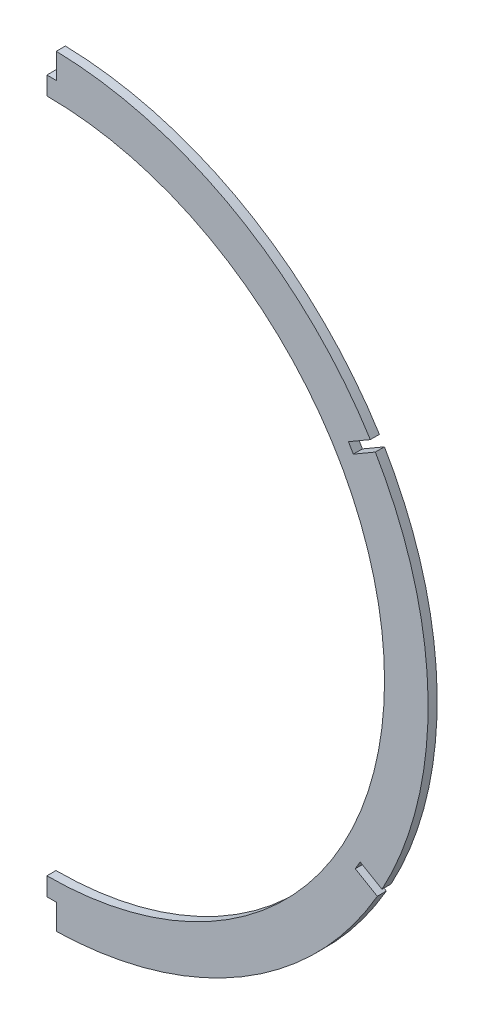
SolidWorks part; units mm, degrees
material "Plywood"
ref_plane "Front Plane" through (0, 0, 0) normal (0, 0, 1) x (1, 0, 0)
ref_plane "Top Plane" through (0, 0, 0) normal (0, 1, 0) x (1, 0, 0)
ref_plane "Right Plane" through (0, 0, 0) normal (1, 0, 0) x (0, 0, -1)
sketch "Sketch1" plane through (0, 0, 0) normal (0, 0, 1) x (1, 0, 0)
  line L0 (0, -110.0909) -> (0, -70.6286) construction
  line L1 (0, 0) -> (0, 245.1538) construction
  line L2 (0, 0) -> (0, 631.6453) construction
  line L3 (-120.188, -34.2725) -> (-93.2472, -61.2132)
  line L4 (0, 0) -> (-284.8905, 0) construction
  line L5 (-93.2472, -61.2132) -> (-94.2927, -70.7977)
  line L8 (-93.2472, -61.2132) -> (-57.7675, -96.693) construction
  arc A0 (-57.7675, -96.693) -> (-120.188, -34.2725) centre (0, 23.495) ccw
  arc A2 (-120.188, -34.2725) -> (-57.7675, -96.693) centre (0, 23.495) ccw construction
  arc A3 (-94.2927, -70.7977) -> (-57.7675, -96.693) centre (0, 23.495) ccw
  point P2 (0, 156.7839)
  point P3 (0, -109.8059)
  point P15 (-93.2472, -61.2132)
  dimension "D1" = 266.5898
  dimension "D2" = 266.7
  dimension "D3" = 23.495
  dimension "D5" = 109.22
  dimension "D6" = 45
  dimension "D7" = 38.1
extrude "Boss-Extrude1" add sketch "Sketch1" along normal mid plane 3.175
sketch "Sketch2" plane through (0, 0, 1.5875) normal (0, 0, 1) x (1, 0, 0)
  line L4 (-77.3048, -55.603) -> (-78.3203, -64.9126)
  line L5 (-107.5191, -25.3887) -> (-77.3048, -55.603)
  line L6 (-77.3048, -55.603) -> (-78.3203, -64.9126)
  line L7 (-107.5191, -25.3887) -> (-77.3048, -55.603)
  arc A2 (-78.3203, -64.9126) -> (-107.5191, -25.3887) centre (0, 23.495) ccw
  arc A3 (-78.3203, -64.9126) -> (-107.5191, -25.3887) centre (0, 23.495) ccw
  dimension "D1" = 15.24
extrude "Cut-Extrude1" cut sketch "Sketch2" against normal up to surface (3.175 mm away) up to face at (-30.5678, -4.3762, -1.5875)
fillet "Fillet1" radius 8.89 6 edges at (-107.5191, -25.3887, 0) (-120.188, -34.2725, 0) (-94.2927, -70.7977, 0) (-93.2472, -61.2132, 0) (-77.3048, -55.603, 0) (-78.3203, -64.9126, 0)
sketch "Sketch3" plane through (0, 0, 0) normal (1, 0, 0) x (0, 0, -1)
  line L1 (-107.0531, 227.715) -> (127.3903, 227.715)
  line L2 (-107.0531, 227.715) -> (-107.0531, -194.8481)
  line L3 (-107.0531, -194.8481) -> (127.3903, -194.8481)
  line L4 (127.3903, 227.715) -> (127.3903, -194.8481)
extrude "Cut-Extrude2" cut sketch "Sketch3" against normal through all
sketch "Sketch4" plane through (0, 0, -1.5875) normal (0, 0, -1) x (-1, 0, 0)
  line L0 (0, 0) -> (0, 141.605) construction
  line L1 (0, 141.605) -> (0, 147.955) construction
  line L2 (-3.302, 147.955) -> (3.302, 147.955)
  line L3 (0, 147.955) -> (0, 160.655)
  line L4 (3.302, 147.955) -> (3.302, 160.655)
  line L5 (-3.302, 160.655) -> (3.302, 160.655)
  line L6 (100.8525, 84.9665) -> (106.3397, 88.1623) construction
  line L7 (105.4896, 89.6219) -> (107.1898, 86.7027)
  line L8 (100.8525, 84.9665) -> (0, 26.2278) construction
  line L9 (105.4896, 89.6219) -> (116.464, 96.0136)
  line L10 (107.1898, 86.7027) -> (118.1641, 93.0944)
  line L11 (116.464, 96.0136) -> (118.1641, 93.0944)
  line L12 (100.5646, -32.3432) -> (108.7167, -37.0911) construction
  line L13 (0, 26.2278) -> (100.5646, -32.3432) construction
  line L14 (107.8666, -38.5507) -> (109.5668, -35.6316)
  line L15 (107.8666, -38.5507) -> (117.8184, -44.3469)
  line L16 (109.5668, -35.6316) -> (119.5186, -41.4277)
  line L17 (117.8184, -44.3469) -> (119.5186, -41.4277)
  line L18 (0, 26.2278) -> (0, -94.615) construction
  line L19 (0, -94.615) -> (0, -100.965) construction
  line L20 (-3.302, -100.965) -> (3.302, -100.965)
  line L21 (0, -100.965) -> (0, -113.665)
  line L22 (3.302, -100.965) -> (3.302, -113.665)
  line L23 (-3.302, -113.665) -> (3.302, -113.665)
  line L24 (0, 26.2278) -> (-100.5646, -32.3432) construction
  line L25 (-100.5646, -32.3432) -> (-108.7167, -37.0911) construction
  line L26 (-100.8525, 84.9665) -> (0, 26.2278) construction
  line L27 (-100.8525, 84.9665) -> (-106.3397, 88.1623) construction
  line L28 (-3.302, -100.965) -> (-3.302, -113.665)
  line L29 (-117.8184, -44.3469) -> (-119.5186, -41.4277)
  line L30 (-109.5668, -35.6316) -> (-119.5186, -41.4277)
  line L31 (-107.8666, -38.5507) -> (-117.8184, -44.3469)
  line L32 (-107.8666, -38.5507) -> (-109.5668, -35.6316)
  line L33 (-116.464, 96.0136) -> (-118.1641, 93.0944)
  line L34 (-107.1898, 86.7027) -> (-118.1641, 93.0944)
  line L35 (-105.4896, 89.6219) -> (-116.464, 96.0136)
  line L36 (-105.4896, 89.6219) -> (-107.1898, 86.7027)
  line L37 (-3.302, 147.955) -> (-3.302, 160.655)
  point P2 (-103.2295, -33.8953)
  point P39 (108.7167, -37.0911)
  arc M26 (0, 156.845) -> (0, -109.855) centre (0, 23.495) ccw
  line M27 (0, -109.855) -> (0, -94.615)
  line M29 (0, 141.605) -> (0, 156.845)
  dimension "D1" = 26.2278
  dimension "D2" = 59.783
  dimension "D3" = 59.783
  dimension "D4" = 116.711
  dimension "D5" = 6.35
  dimension "D6" = 12.7
  dimension "D7" = 3.3782
  dimension "D8" = 141.605
  dimension "D9" = 6.35
  dimension "D10" = 3.302
  dimension "D11" = 12.7
  dimension "D12" = 6.35
  dimension "D13" = 120.8428
  dimension "D14" = 3.302
  dimension "D15" = 12.7
  dimension "D16" = 116.3778
  dimension "D17" = 119.4618
  dimension "D18" = 6.35
  dimension "D19" = 3.3782
extrude "Cut-Extrude3" cut sketch "Sketch4" against normal through all contours L37 L2 M29 M26 | L36 L35 L34 M26 | L31 L32 L30 M26 | L20 L28 M26 M27
